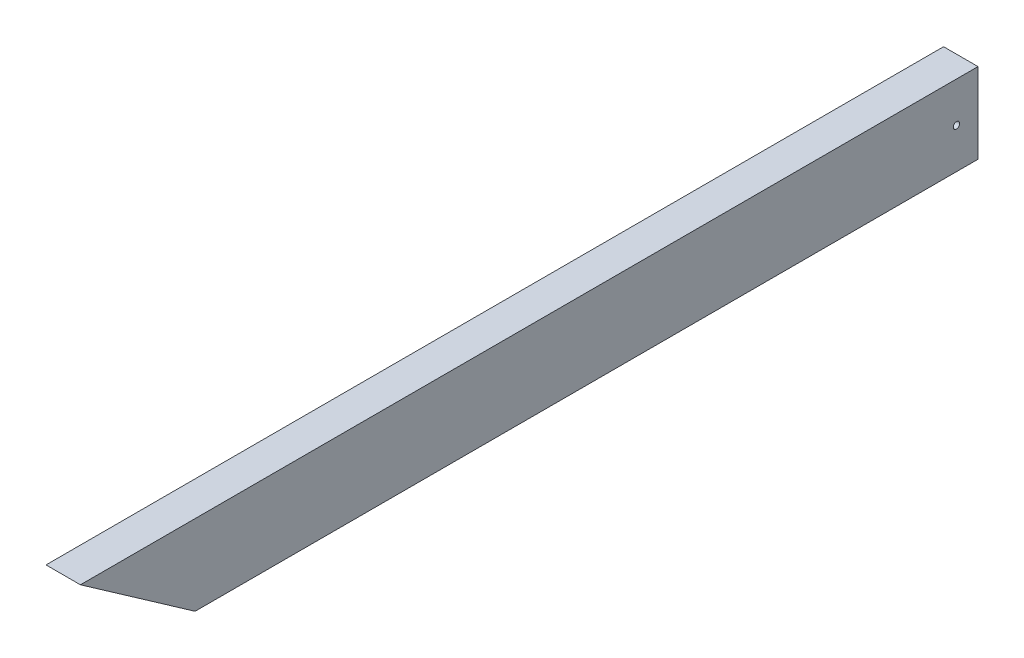
SolidWorks part; units mm, degrees
material "Pine"
ref_plane "Front Plane" through (0, 0, 0) normal (0, 0, 1) x (1, 0, 0)
ref_plane "Top Plane" through (0, 0, 0) normal (0, 1, 0) x (1, 0, 0)
ref_plane "Right Plane" through (0, 0, 0) normal (1, 0, 0) x (0, 0, -1)
sketch "Sketch1" plane through (0, 0, 0) normal (0, 0, 1) x (1, 0, 0)
  line L1 (-19.05, -44.45) -> (19.05, -44.45)
  line L2 (-19.05, -44.45) -> (-19.05, 44.45)
  line L3 (-19.05, 44.45) -> (19.05, 44.45)
  line L4 (19.05, -44.45) -> (19.05, 44.45)
  line L5 (-19.05, -44.45) -> (19.05, 44.45) construction
  line L6 (-19.05, 44.45) -> (19.05, -44.45) construction
  point P0 (0, 0)
  dimension "D1" = 88.9
  dimension "D2" = 38.1
extrude "Boss-Extrude1" add sketch "Sketch1" along normal blind 1143
sketch "Sketch2" plane through (19.05, 0, 0) normal (1, 0, 0) x (0, 0, -1)
  line L0 (-1143, -44.45) -> (-1143, 44.45) construction
  line L1 (0, -44.45) -> (0, 44.45) construction
  point P0 (-1128.7125, 0)
  point P1 (-23.8125, 0)
  dimension "D1" = 14.2875
  dimension "D2" = 23.8125
hole_wizard "9/32 (0.28125) Diameter Hole1" positions "Sketch3" profile "Sketch4" hole size "9/32" standard "ANSI Inch" end condition through all
sketch "Sketch3" plane through (19.05, 0, 0) normal (1, 0, 0) x (0, 0, -1)
  point P0 (-1128.7125, 0)
  point P3 (-23.8125, 0)
sketch "Sketch4" plane through (19.05, 0, 1128.7125) normal (0, 1, 0) x (0, 0, -1)
  line L0 (0, 0) -> (0, 38.1)
  line L1 (0, 38.1) -> (3.5719, 38.1)
  line L2 (3.5719, 38.1) -> (3.5719, 0)
  line L5 (3.5719, 0) -> (0, 0)
  line L11 (0, -6.35) -> (0, 107.95) construction
  dimension "Thru Hole Dia." = 7.1437
  dimension "Thru Hole Depth" = 38.1
sketch "Sketch5" plane through (19.05, 0, 0) normal (1, 0, 0) x (0, 0, -1)
  line L1 (-1143, -44.45) -> (0, -44.45) construction
  line L2 (-993.775, 44.45) -> (-866.8126, -44.45)
  line L3 (0, -44.45) -> (0, 44.45) construction
  line L4 (-869.95, -44.45) -> (-866.8126, -44.45)
  line L6 (-1143, 44.45) -> (0, 44.45) construction
  circle M2 centre (-1128.7125, 0) radius 3.5719
  line M5 (0, 44.45) -> (-1143, 44.45)
  line M6 (-1143, 44.45) -> (-1143, -44.45)
  line M7 (-1143, -44.45) -> (0, -44.45)
  dimension "D1" = 35
  dimension "D2" = 993.775
extrude "Cut-Extrude1" cut sketch "Sketch5" against normal through all contours L2 M5 M6 M7 M2
